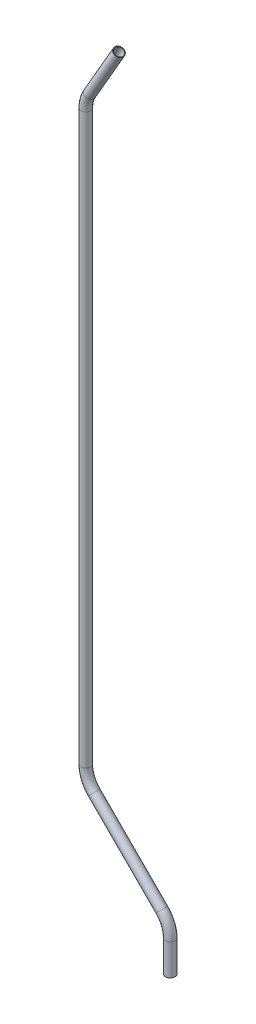
SolidWorks part; units mm, degrees
ref_plane "Front Plane" through (0, 0, 0) normal (0, 0, 1) x (1, 0, 0)
ref_plane "Top Plane" through (0, 0, 0) normal (0, 1, 0) x (1, 0, 0)
ref_plane "Right Plane" through (0, 0, 0) normal (1, 0, 0) x (0, 0, -1)
sketch "Sketch1" plane through (0, 0, 0) normal (0, 0, 1) x (1, 0, 0)
  line L0 (0, -253.638) -> (0, -196.488) construction
  line L2 (0, -196.488) -> (-111.76, -196.488) construction
  line L3 (-111.76, -196.488) -> (-111.76, 693.0535) construction
  line L4 (-111.76, 693.0535) -> (-67.7659, 769.2535) construction
  line L5 (0, -196.488) -> (-111.76, -84.728) construction
  line L6 (0, -253.638) -> (0, -212.2696)
  line L7 (-11.1592, -185.3288) -> (-100.6008, -95.8873)
  line L8 (-111.76, -68.9465) -> (-111.76, 682.8446)
  line L9 (-106.6556, 701.8946) -> (-67.7659, 769.2535)
  arc A0 (0, -212.2696) -> (-11.1592, -185.3288) centre (-38.1, -212.2696) ccw
  arc A1 (-111.76, -68.9465) -> (-100.6008, -95.8873) centre (-73.66, -68.9465) ccw
  arc A2 (-111.76, 682.8446) -> (-106.6556, 701.8946) centre (-73.66, 682.8446) cw
  dimension "D5" = 38.1
  dimension "D6" = 38.1
  dimension "D9" = 38.1
  dimension "D1" = 30
  dimension "D2" = 45
  dimension "D3" = 57.15
  dimension "D4" = 111.76
  dimension "D7" = 76.2
  dimension "D8" = 762
sketch "Sketch2" plane through (0, 0, 0) normal (0, 1, 0) x (1, 0, 0)
  circle A1 centre (-111.76, 0) radius 6.35
  circle A2 centre (-111.76, 0) radius 5.5372
  dimension "D1" = 12.7
  dimension "D2" = 0.8128
sweep "Sweep1" add profiles "Sketch2" path "Sketch1"
